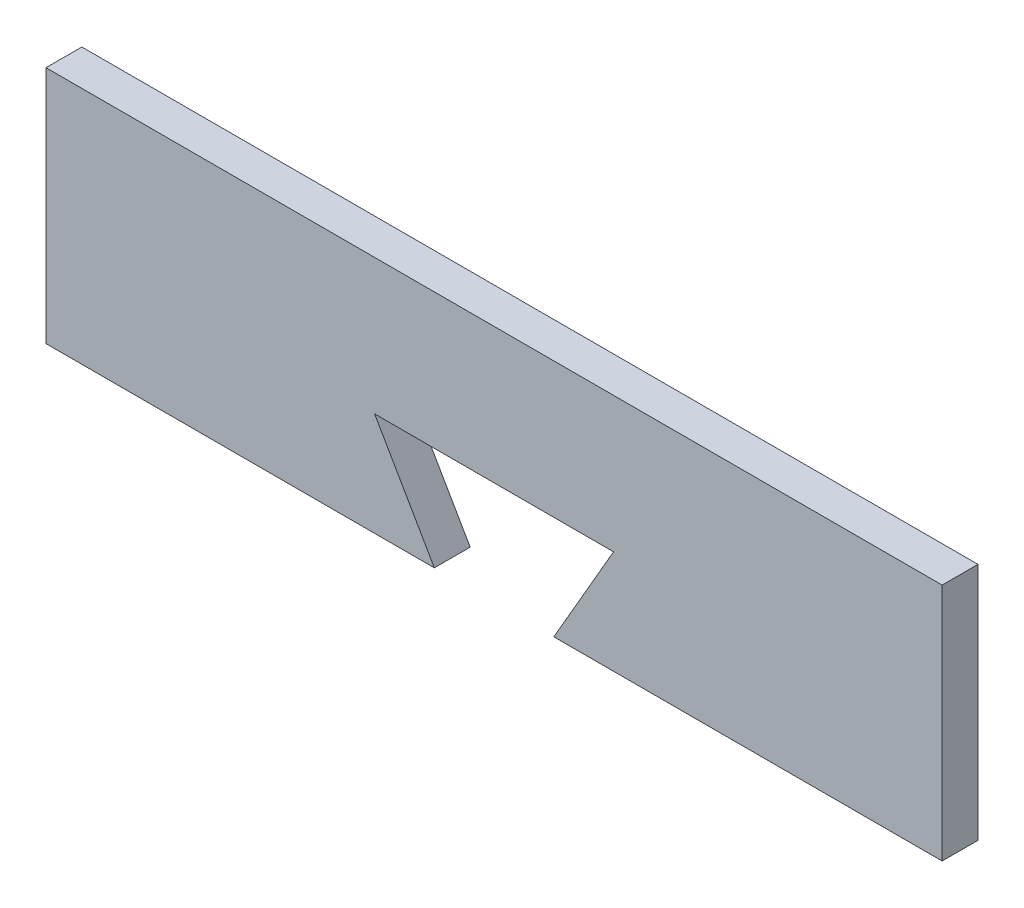
SolidWorks part; units mm, degrees
ref_plane "Plan de face" through (0, 0, 0) normal (0, 0, 1) x (1, 0, 0)
ref_plane "Plan de dessus" through (0, 0, 0) normal (0, 1, 0) x (1, 0, 0)
ref_plane "Plan de droite" through (0, 0, 0) normal (1, 0, 0) x (0, 0, -1)
sketch "Esquisse1" plane through (0, 0, 0) normal (0, 0, 1) x (1, 0, 0)
  line L0 (-84.8349, 29.1221) -> (65.1651, 29.1221)
  line L1 (65.1651, 29.1221) -> (65.1651, -10.8779)
  line L2 (65.1651, -10.8779) -> (0.1651, -10.8779)
  line L3 (0.1651, -10.8779) -> (10.1651, 6.4426)
  line L4 (10.1651, 6.4426) -> (-29.8349, 6.4426)
  line L5 (-29.8349, 6.4426) -> (-19.8349, -10.8779)
  line L6 (-19.8349, -10.8779) -> (-84.8349, -10.8779)
  line L7 (-84.8349, -10.8779) -> (-84.8349, 29.1221)
  dimension "D1" = 150
  dimension "D2" = 40
  dimension "D3" = 40
  dimension "D4" = 65
  dimension "D5" = 65
  dimension "D6" = 20
  dimension "D7" = 20
  dimension "D8" = 20
  dimension "D9" = 40
extrude "Boss.-Extru.1" add sketch "Esquisse1" along normal blind 6
